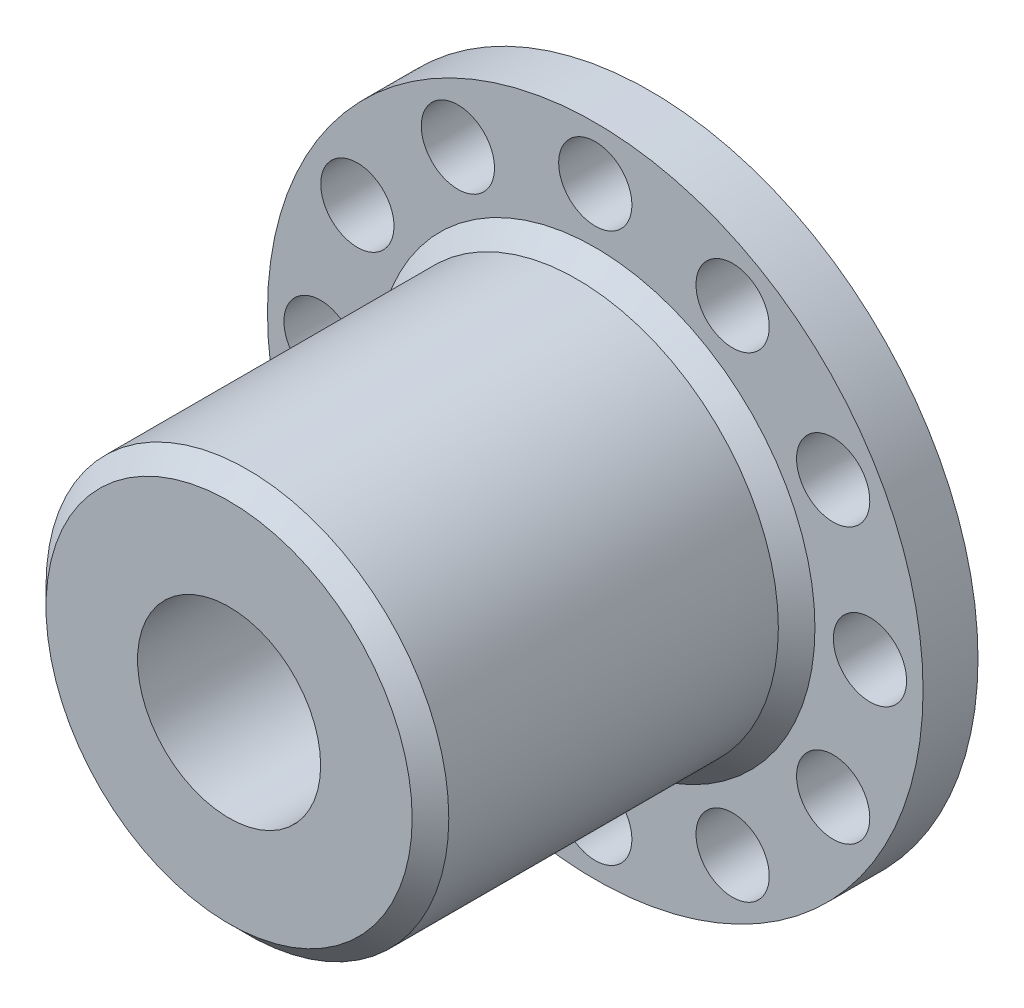
SolidWorks part; units mm, degrees
ref_plane "Front Plane" through (0, 0, 0) normal (0, 0, 1) x (1, 0, 0)
ref_plane "Top Plane" through (0, 0, 0) normal (0, 1, 0) x (1, 0, 0)
ref_plane "Right Plane" through (0, 0, 0) normal (1, 0, 0) x (0, 0, -1)
sketch "Sketch1" plane through (0, 0, 0) normal (0, 0, 1) x (1, 0, 0)
  circle A0 centre (0, 0) radius 17.9043
  circle A1 centre (0, 0) radius 17.9043 construction
extrude "Boss-Extrude1" add sketch "Sketch1" along normal blind 3
sketch "Sketch2" plane through (0, 0, 3) normal (0, 0, 1) x (1, 0, 0)
  circle A0 centre (0, 0) radius 11
  dimension "D1" = 22
extrude "Boss-Extrude2" add sketch "Sketch2" along normal blind 20
sketch "Sketch3" plane through (0, 0, 23) normal (0, 0, 1) x (1, 0, 0)
  circle A0 centre (0, 0) radius 5
  dimension "D1" = 10
extrude "Cut-Extrude1" cut sketch "Sketch3" against normal through all
sketch "Sketch4" plane through (0, 0, 0) normal (0, 1, 0) x (1, 0, 0)
  circle A0 centre (0, -15) radius 2
  dimension "D1" = 4
  dimension "D2" = 15
extrude "Cut-Extrude2" cut sketch "Sketch4" against normal blind 15
chamfer "Chamfer1" distance 1 angle 45 2 edges at (11, 0, 3) (11, 0, 23)
sketch "Sketch5" plane through (0, 0, 3) normal (0, 0, 1) x (1, 0, 0)
  circle A0 centre (7.5022, 12.9941) radius 2
  circle A1 centre (0, 0) radius 17.9043
  circle A2 centre (0, 0) radius 17.9043
  dimension "D2" = 4
  dimension "D1" = 0
extrude "Cut-Extrude5" cut sketch "Sketch5" against normal through all contours A0
pattern_circular "CirPattern2" count 12 over 360 about axis through (0, 0, 0) along (0, 0, 1) of "Cut-Extrude5"
scale "Scale1" scale about origin uniform scaling yes scale factor 0.630435
